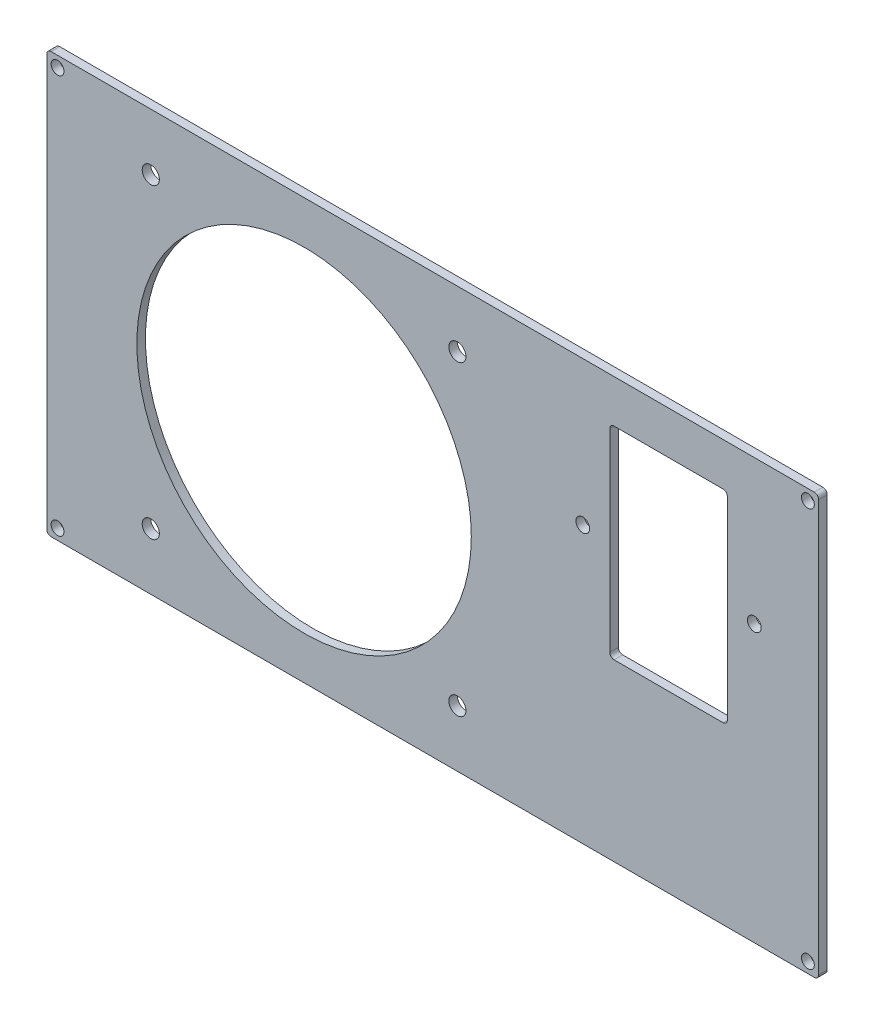
SolidWorks part; units mm, degrees
ref_plane "Спереди" through (0, 0, 0) normal (0, 0, 1) x (1, 0, 0)
ref_plane "Сверху" through (0, 0, 0) normal (0, 1, 0) x (1, 0, 0)
ref_plane "Справа" through (0, 0, 0) normal (1, 0, 0) x (0, 0, -1)
other "Configuration Table"
sketch "Эскиз1" plane through (0, 0, 0) normal (0, 0, 1) x (1, 0, 0)
  line L0 (0, 49) -> (180, 49) construction
  line L1 (0, 0) -> (180, 0)
  line L2 (0, 0) -> (0, 98)
  line L3 (0, 98) -> (180, 98)
  line L4 (180, 0) -> (180, 98)
  line L5 (0, 2.5) -> (180, 2.5) construction
  line L6 (0, 95.5) -> (180, 95.5) construction
  line L7 (2.5, 98) -> (2.5, 0) construction
  line L8 (177.5, 98) -> (177.5, 0) construction
  line L9 (125, 64.4) -> (165, 64.4) construction
  line L10 (24.25, 84.75) -> (95.75, 84.75) construction
  line L11 (24.25, 84.75) -> (24.25, 13.25) construction
  line L12 (24.25, 13.25) -> (95.75, 13.25) construction
  line L13 (95.75, 84.75) -> (95.75, 13.25) construction
  line L14 (24.25, 84.75) -> (95.75, 13.25) construction
  line L15 (24.25, 13.25) -> (95.75, 84.75) construction
  line L16 (131.3, 88) -> (158.7, 88)
  line L17 (131.3, 88) -> (131.3, 40.8)
  line L18 (131.3, 40.8) -> (158.7, 40.8)
  line L19 (158.7, 88) -> (158.7, 40.8)
  line L20 (131.3, 88) -> (158.7, 40.8) construction
  line L21 (131.3, 40.8) -> (158.7, 88) construction
  circle A0 centre (2.5, 95.5) radius 1.5
  circle A1 centre (177.5, 95.5) radius 1.5
  circle A2 centre (177.5, 2.5) radius 1.5
  circle A3 centre (2.5, 2.5) radius 1.5
  circle A4 centre (60, 49) radius 39
  circle A5 centre (24.25, 84.75) radius 2
  circle A6 centre (95.75, 84.75) radius 2
  circle A7 centre (95.75, 13.25) radius 2
  circle A8 centre (24.25, 13.25) radius 2
  circle A11 centre (125, 64.4) radius 1.6
  circle A12 centre (165, 64.4) radius 1.6
  point P23 (60, 49)
  point P34 (145, 64.4)
  dimension "D7" = 3
  dimension "D8" = 3
  dimension "D9" = 3
  dimension "D10" = 3
  dimension "D14" = 78
  dimension "D15" = 4
  dimension "D16" = 4
  dimension "D17" = 4
  dimension "D18" = 4
  dimension "D22" = 20
  dimension "D23" = 20
  dimension "D24" = 3.2
  dimension "D25" = 3.2
  dimension "D1" = 180
  dimension "D2" = 98
  dimension "D3" = 2.5
  dimension "D4" = 2.5
  dimension "D5" = 2.5
  dimension "D6" = 2.5
  dimension "D11" = 71.5
  dimension "D12" = 71.5
  dimension "D13" = 60
  dimension "D19" = 47.2
  dimension "D20" = 27.4
  dimension "D21" = 35
  dimension "D26" = 10
extrude "Бобышка-Вытянуть1" add sketch "Эскиз1" along normal blind 2
fillet "Скругление1" radius 1 4 edges at (0, 98, 1) (0, 0, 1) (180, 0, 1) (180, 98, 1)
fillet "Скругление2" radius 1 4 edges at (158.7, 88, 1) (131.3, 88, 1) (131.3, 40.8, 1) (158.7, 40.8, 1)
